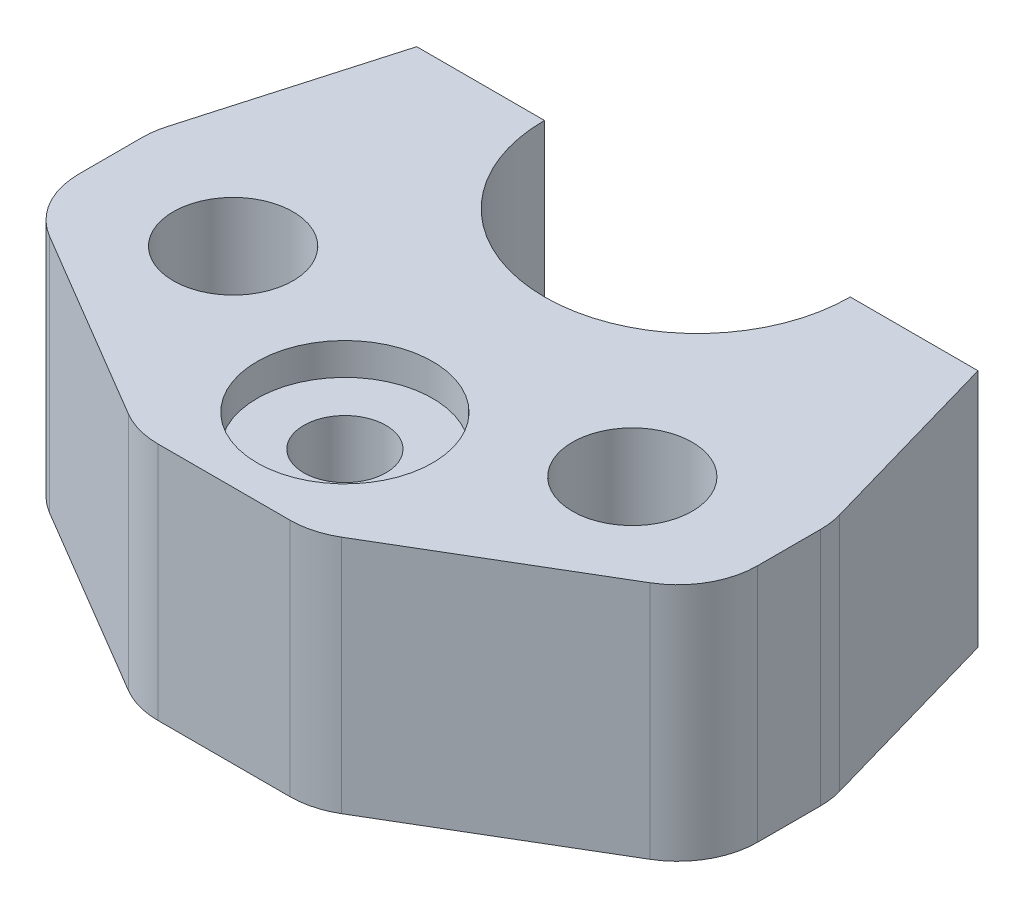
SolidWorks part; units mm, degrees
ref_plane "Front Plane" through (0, 0, 0) normal (0, 0, 1) x (1, 0, 0)
ref_plane "Top Plane" through (0, 0, 0) normal (0, 1, 0) x (1, 0, 0)
ref_plane "Right Plane" through (0, 0, 0) normal (1, 0, 0) x (0, 0, -1)
sketch "Sketch2" plane through (0, 0, 0) normal (0, 1, 0) x (1, 0, 0)
  line L0 (0, -19.15) -> (0, -59.3) construction
  line L1 (35.15, 0) -> (19.15, 0)
  line L2 (-35.15, 0) -> (-42.5, -25.65)
  line L3 (-42.5, -25.65) -> (-42.5, -40.65)
  line L4 (-42.5, -40.65) -> (-11, -59.3)
  line L5 (-11, -59.3) -> (11, -59.3)
  line L6 (42.5, -40.65) -> (11, -59.3)
  line L7 (42.5, -25.65) -> (42.5, -40.65)
  line L8 (35.15, 0) -> (42.5, -25.65)
  line L9 (-19.15, 0) -> (-35.15, 0)
  arc A0 (-19.15, 0) -> (19.15, 0) centre (0, 0) ccw
  circle A1 centre (-25, -33.15) radius 7.5
  circle A2 centre (25, -33.15) radius 7.5
  circle A3 centre (0, -44.15) radius 11
  circle A4 centre (0, -44.15) radius 5.15
  point P12 (0, -19.15)
  point P19 (-25, -25.65)
  point P24 (0, -55.15)
  point P25 (0, -49.3)
  point P26 (-32.5, -33.15)
  dimension "D1" = 19.15
  dimension "D2" = 15
  dimension "D3" = 22
  dimension "D4" = 10.3
  dimension "D5" = 11
  dimension "D6" = 50
  dimension "D7" = 25
  dimension "D8" = 16
  dimension "D9" = 10
  dimension "D10" = 15
  dimension "D11" = 10
  dimension "D12" = 22
extrude "Boss-Extrude1" add sketch "Sketch2" along normal blind 30 contours L0 A0 L9 L2 L3 L4 L5 A3 A1 | A0 L0 A3 L5 L6 L7 L8 L1 A2 | A3 L0 A4 | L0 A3 A4
fillet "Fillet1" radius 10 6 edges at (-42.5, 15, 25.65) (-42.5, 15, 40.65) (42.5, 15, 25.65) (42.5, 15, 40.65) (11, 15, 59.3) (-11, 15, 59.3)
sketch "Sketch4" plane through (0, 30, 0) normal (0, 1, 0) x (1, 0, 0)
  circle A0 centre (0, -44.15) radius 11
  dimension "D1" = 22
extrude "Cut-Extrude1" cut sketch "Sketch4" against normal blind 4
